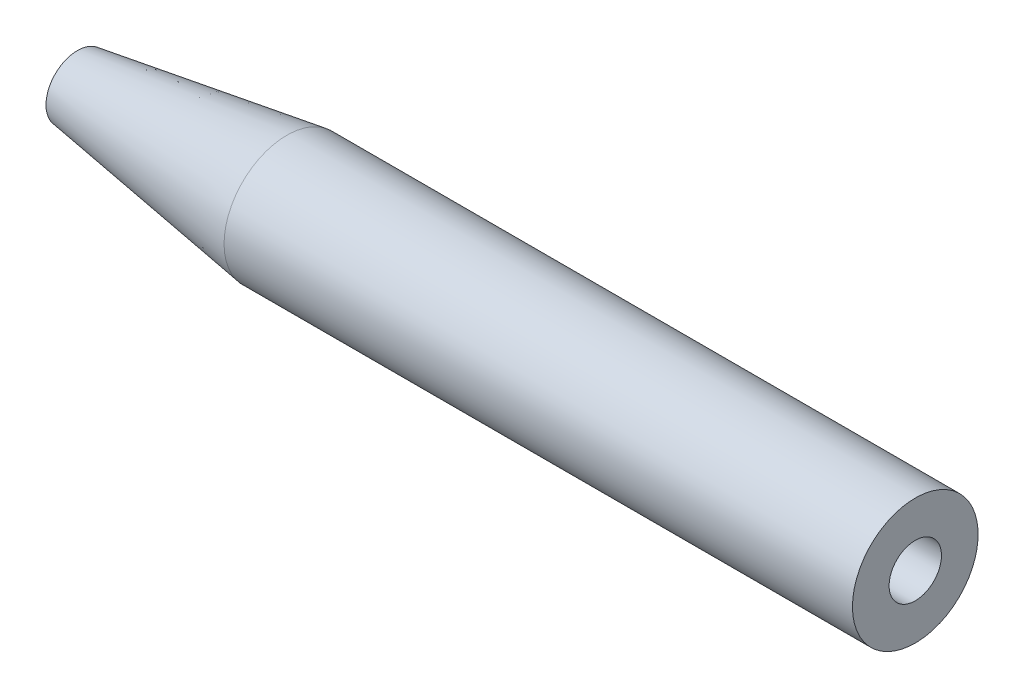
SolidWorks part; units mm, degrees
material "PA Type 6"
ref_plane "Front Plane" through (0, 0, 0) normal (0, 0, 1) x (1, 0, 0)
ref_plane "Top Plane" through (0, 0, 0) normal (0, 1, 0) x (1, 0, 0)
ref_plane "Right Plane" through (0, 0, 0) normal (1, 0, 0) x (0, 0, -1)
sketch "Sketch1" plane through (0, 0, 0) normal (0, 1, 0) x (1, 0, 0)
  line L0 (0, 0) -> (1.985, 0) construction
  line L1 (0, 0) -> (0, 3)
  line L2 (0, 3) -> (-30, 3)
  line L3 (-30, 3) -> (-40, 1.5)
  line L4 (-40, 1.5) -> (-40, 0)
  line L5 (-40, 0) -> (0, 0)
  dimension "D1" = 10
  dimension "Length" = 40
  dimension "Dia" = 6
  dimension "D2" = 3
revolve "Revolve1" add sketch "Sketch1" angle 360 about L0
hole_wizard "M3x0.5 Tapped Hole1" positions "Sketch2" profile "Sketch3" tap size "M3x0.5" standard "ANSI Metric"
sketch "Sketch2" plane through (0, 0, 0) normal (1, 0, 0) x (0, 0, -1)
  point P0 (0, 0)
sketch "Sketch3" plane through (0, 0, 0) normal (0, 1, 0) x (0, 0, -1)
  line L0 (0, 0) -> (0, 9.5)
  line L1 (0, 9.5) -> (1.25, 8.7489)
  line L2 (1.25, 8.7489) -> (1.25, 0)
  line L5 (1.25, 0) -> (0, 0)
  line L10 (0, 9.5) -> (-1.25, 8.7489) construction
  line L11 (0, -6.35) -> (0, 107.95) construction
  dimension "Tap Drill Dia." = 2.5
  dimension "Tap Drill Depth" = 9.5
  dimension "Drill Angle" = 118
cosmetic thread "Hole Thread1" parameters "D1"=8, "D2"=3
